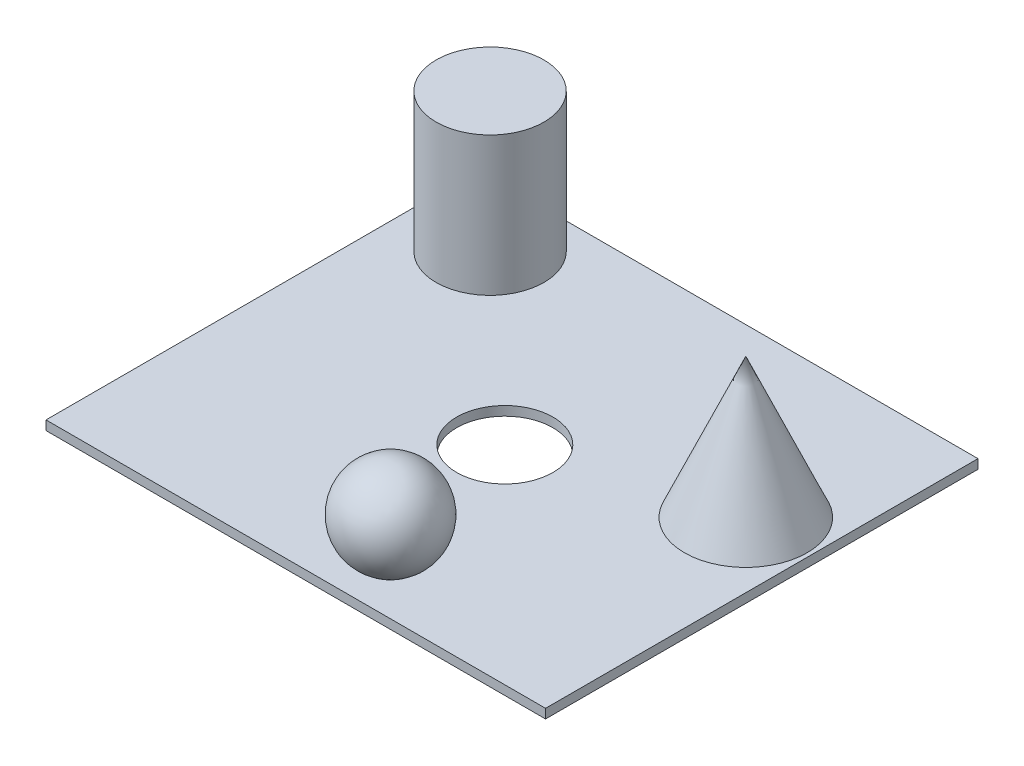
SolidWorks part; units mm, degrees
ref_plane "前视基准面" through (0, 0, 0) normal (0, 0, 1) x (1, 0, 0)
ref_plane "上视基准面" through (0, 0, 0) normal (0, 1, 0) x (1, 0, 0)
ref_plane "右视基准面" through (0, 0, 0) normal (1, 0, 0) x (0, 0, -1)
sketch "草图1" plane through (0, 0, 0) normal (0, 1, 0) x (1, 0, 0)
  line L1 (-63.8958, 36.0505) -> (43.9938, 36.0505)
  line L2 (-63.8958, 36.0505) -> (-63.8958, -57.3491)
  line L3 (-63.8958, -57.3491) -> (43.9938, -57.3491)
  line L4 (43.9938, 36.0505) -> (43.9938, -57.3491)
extrude "凸台-拉伸1" add sketch "草图1" along normal blind 2
sketch "草图2" plane through (0, 2, 0) normal (0, 1, 0) x (1, 0, 0)
  circle A0 centre (-47.4611, 22.1196) radius 11.6398
extrude "凸台-拉伸2" add sketch "草图2" along normal blind 30
sketch "草图3" plane through (0, 2, 0) normal (0, 1, 0) x (1, 0, 0)
  circle A0 centre (-9.6992, -12.4535) radius 10.3882
extrude "切除-拉伸1" cut sketch "草图3" against normal blind 30
sketch "草图6" plane through (0, 0, 0) normal (1, 0, 0) x (0, 0, -1)
  line L0 (-57.3491, 0) -> (36.0505, 0) construction
  line L1 (-46.8321, 24.0082) -> (-46.8321, -2.1238) construction
  line L2 (-46.8321, 2) -> (-42.4732, 2)
  line L4 (-46.8321, 2) -> (-46.8321, 21)
  arc A0 (-42.4732, 2) -> (-46.8321, 21) centre (-46.8321, 11) ccw
  dimension "D2" = 20
  dimension "D1" = 11
revolve "旋转4" add sketch "草图6" angle 360 about L1
sketch "草图7" plane through (0, 0, 0) normal (0, 0, 1) x (1, 0, 0)
  line L0 (16.6398, 2) -> (29.8977, 32.1417)
  line L1 (-63.8958, 2) -> (43.9938, 2) construction
  line L2 (29.8977, 32.1417) -> (29.8977, 2)
  line L3 (29.8977, 2) -> (16.6398, 2)
revolve "旋转5" add sketch "草图7" angle 360 about L2
